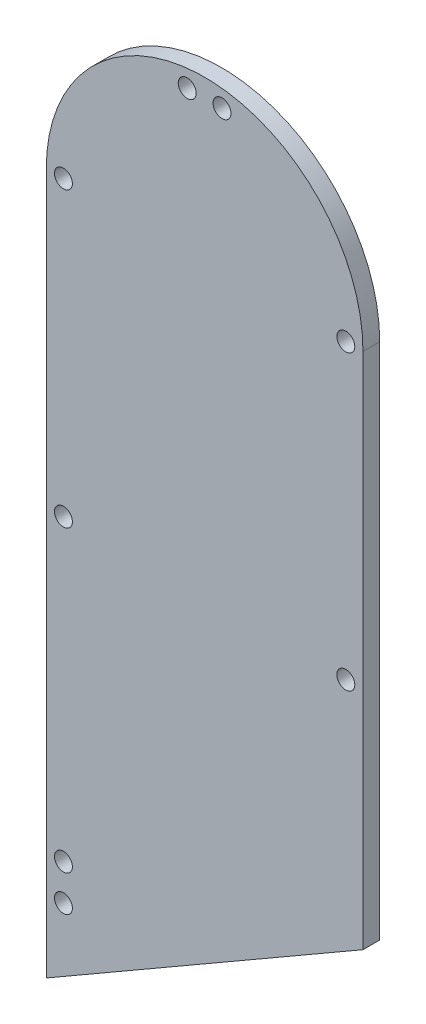
SolidWorks part; units mm, degrees
ref_plane "Front Plane" through (0, 0, 0) normal (0, 0, 1) x (1, 0, 0)
ref_plane "Top Plane" through (0, 0, 0) normal (0, 1, 0) x (1, 0, 0)
ref_plane "Right Plane" through (0, 0, 0) normal (1, 0, 0) x (0, 0, -1)
sketch "Sketch2" plane through (0, 0, 0) normal (0, 0, 1) x (1, 0, 0)
  line L0 (54.5827, -59.5829) -> (54.5827, 171.3946)
  line L1 (-5.4173, 171.3946) -> (-5.4173, -59.5829)
  arc A0 (-5.4173, -59.5829) -> (54.5827, -59.5829) centre (24.5827, -59.5829) ccw
  arc A1 (54.5827, 171.3946) -> (-5.4173, 171.3946) centre (24.5827, 171.3946) ccw
  circle A2 centre (27.8827, 197.9403) radius 1.7
  circle A3 centre (-2.1673, -59.5829) radius 1.7
  circle A4 centre (5.6676, -78.498) radius 1.7
  circle A5 centre (21.1827, -86.116) radius 1.7
  circle A6 centre (51.3327, 171.3946) radius 1.7
  circle A9 centre (-2.1673, 59.3059) radius 1.7
  circle A10 centre (27.9827, -86.116) radius 1.7
  circle A12 centre (-2.1673, 171.3946) radius 1.7
  circle A13 centre (51.3327, 115.9059) radius 1.7
  circle A14 centre (-2.1673, 115.9059) radius 1.7
  circle A16 centre (43.4978, -78.498) radius 1.7
  circle A17 centre (51.3327, -59.5829) radius 1.7
  circle A18 centre (51.3327, -34.0941) radius 1.7
  circle A19 centre (-2.1673, -34.0941) radius 1.7
  circle A20 centre (51.3327, -4.0941) radius 1.7
  circle A21 centre (-2.1673, -4.0941) radius 1.7
  circle A22 centre (51.3327, 25.9059) radius 1.7
  circle A23 centre (-2.1673, 25.9059) radius 1.7
  circle A26 centre (21.2827, 197.9403) radius 1.7
  circle A27 centre (51.3327, 52.5059) radius 1.7
  circle A28 centre (51.3327, 59.3059) radius 1.7
  circle A29 centre (-2.1673, 52.5059) radius 1.7
extrude "Boss-Extrude1" add sketch "Sketch2" along normal blind 3.175
sketch "Sketch3" plane through (0, 0, 3.175) normal (0, 0, 1) x (1, 0, 0)
  line L0 (-23.1786, 28.3308) -> (72.344, 83.4809)
  line L1 (-5.4173, 55.9059) -> (54.5827, 55.9059) construction
  line L2 (-5.4173, 171.3946) -> (-5.4173, -59.5829) construction
  line L3 (54.5827, -59.5829) -> (54.5827, 171.3946) construction
  line L4 (-23.1786, 28.3308) -> (-23.1786, -133.0465)
  line L5 (-23.1786, -133.0465) -> (72.344, -133.0465)
  line L6 (72.344, -133.0465) -> (72.344, 83.4809)
  point P8 (24.5827, 55.9059)
  point P9 (24.5827, 55.9059)
  dimension "D1" = 30
extrude "Cut-Extrude1" cut sketch "Sketch3" against normal through all
